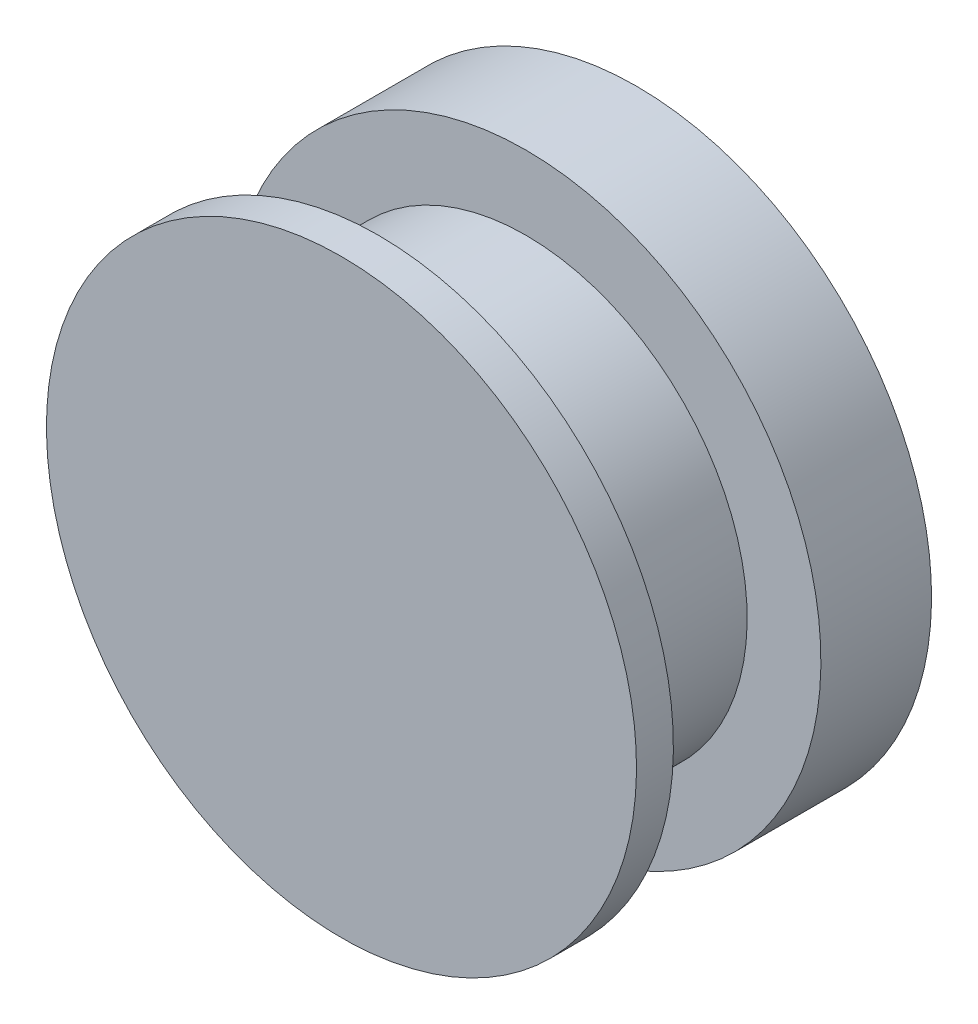
SolidWorks part; units mm, degrees
ref_plane "Front Plane" through (0, 0, 0) normal (0, 0, 1) x (1, 0, 0)
ref_plane "Top Plane" through (0, 0, 0) normal (0, 1, 0) x (1, 0, 0)
ref_plane "Right Plane" through (0, 0, 0) normal (1, 0, 0) x (0, 0, -1)
sketch "Sketch1" plane through (0, 0, 0) normal (1, 0, 0) x (0, 0, -1)
  line L0 (0, 0) -> (0, 2.032)
  line L1 (0, 2.032) -> (0.254, 2.032)
  line L2 (0.254, 2.032) -> (0.254, 1.524)
  line L3 (0.254, 1.524) -> (1.27, 1.524)
  line L4 (1.27, 1.524) -> (1.27, 2.032)
  line L5 (1.27, 2.032) -> (2.032, 2.032)
  line L6 (2.032, 2.032) -> (2.032, 0)
  line L7 (2.032, 0) -> (0, 0)
  dimension "D1" = 0.254
  dimension "D2" = 2.032
  dimension "D3" = 0.762
  dimension "D4" = 1.016
  dimension "D5" = 2.032
  dimension "D6" = 2.032
  dimension "D7" = 1.524
revolve "Revolve1" add sketch "Sketch1" angle 360 about L7
